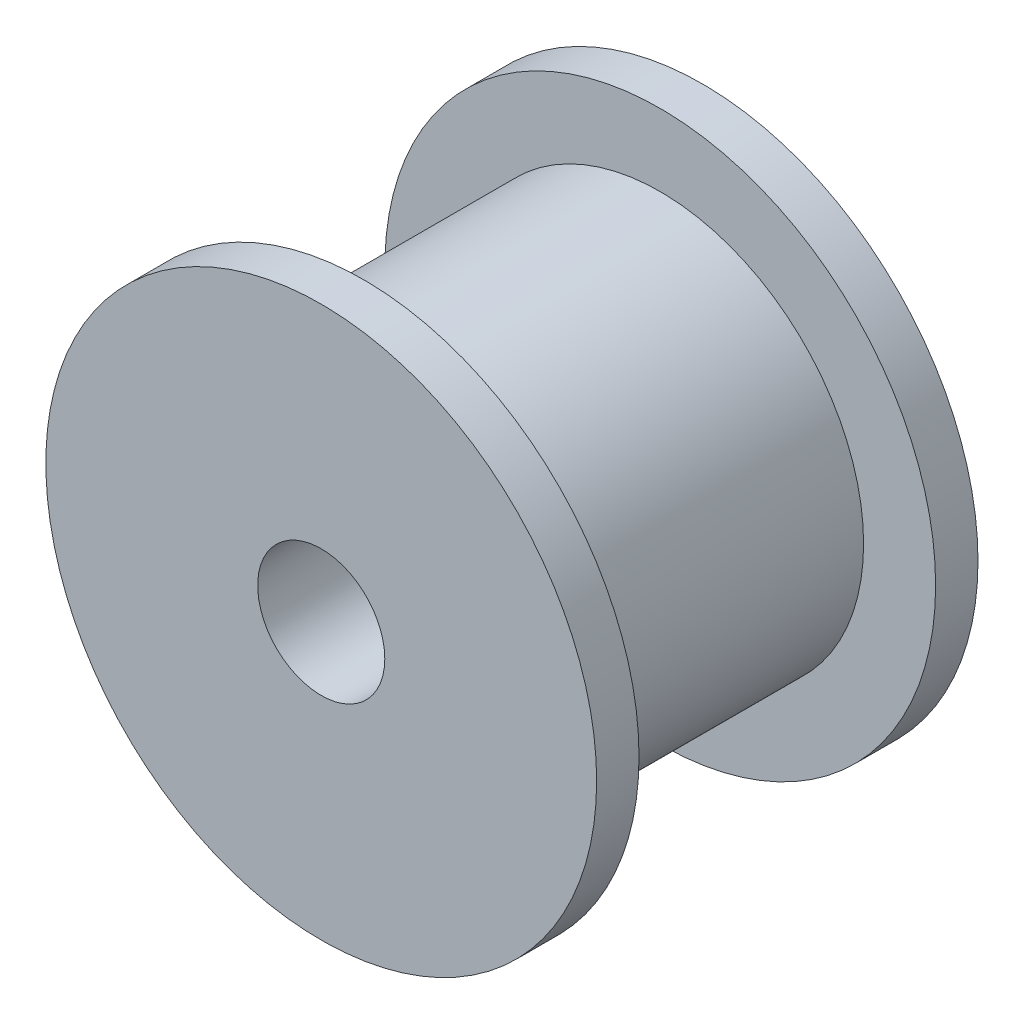
SolidWorks part; units mm, degrees
ref_plane "Front Plane" through (0, 0, 0) normal (0, 0, 1) x (1, 0, 0)
ref_plane "Top Plane" through (0, 0, 0) normal (0, 1, 0) x (1, 0, 0)
ref_plane "Right Plane" through (0, 0, 0) normal (1, 0, 0) x (0, 0, -1)
sketch "Sketch1" plane through (0, 0, 0) normal (0, 0, 1) x (1, 0, 0)
  circle A0 centre (0, 0) radius 6.5
  circle A1 centre (0, 0) radius 1.5
  dimension "D1" = 13
  dimension "D2" = 3
extrude "Boss-Extrude1" add sketch "Sketch1" along normal blind 1
sketch "Sketch2" plane through (0, 0, 1) normal (0, 0, 1) x (1, 0, 0)
  circle A0 centre (0, 0) radius 1.5
  circle A1 centre (0, 0) radius 4.8
  dimension "D1" = 3
  dimension "D2" = 9.6
extrude "Boss-Extrude2" add sketch "Sketch2" along normal blind 7
sketch "Sketch3" plane through (0, 0, 8) normal (0, 0, 1) x (1, 0, 0)
  circle A0 centre (0, 0) radius 1.5
  circle A1 centre (0, 0) radius 6.5
  dimension "D1" = 13
  dimension "D2" = 3
extrude "Boss-Extrude3" add sketch "Sketch3" along normal blind 1
